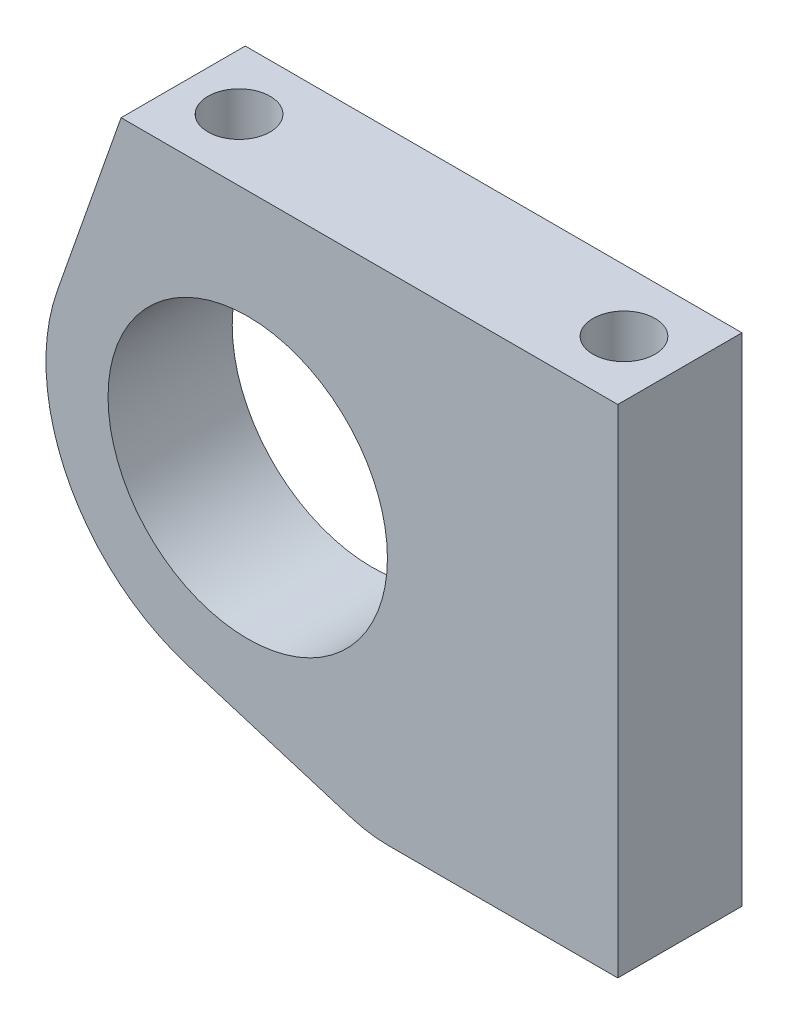
SolidWorks part; units mm, degrees
ref_plane "Front" through (0, 0, 0) normal (0, 0, 1) x (1, 0, 0)
ref_plane "Top" through (0, 0, 0) normal (0, 1, 0) x (1, 0, 0)
ref_plane "Right" through (0, 0, 0) normal (1, 0, 0) x (0, 0, -1)
sketch "Sketch1" plane through (0, 0, 0) normal (0, 0, 1) x (1, 0, 0)
  line L0 (0, 0) -> (50.8, 0) construction
  line L5 (0, 50.8) -> (50.8, 50.8)
  line L6 (0, 50.8) -> (-6.518, 32.2373)
  line L7 (50.8, 50.8) -> (50.8, 0)
  line L8 (50.8, 0) -> (27.3027, 0)
  line L9 (23.5809, 0.5576) -> (6.9061, 5.6686)
  circle A0 centre (12.954, 25.4) radius 6.35
  circle A1 centre (12.954, 25.4) radius 14.2875
  circle A2 centre (12.954, 25.4) radius 20.6375
  arc A3 (23.5809, 0.5576) -> (27.3027, 0) centre (27.3027, 12.7) ccw
  point P11 (12.954, 46.0375)
  point P20 (25.4, 0)
  dimension "D2" = 12.7
  dimension "D5" = 28.575
  dimension "D8" = 25.4
  dimension "D9" = 12.7
  dimension "D1" = 50.8
  dimension "D3" = 25.4
  dimension "D4" = 37.846
  dimension "D7" = 50.8
  dimension "D10" = 50.8
  dimension "D6" = 6.35
extrude "Boss-Extrude2" add sketch "Sketch1" along normal blind 12.7
sketch "Sketch3" plane through (0, 50.8, 0) normal (0, 1, 0) x (1, 0, 0)
  line L0 (0, -6.35) -> (50.8, -6.35) construction
  line L1 (0, -12.7) -> (0, 0) construction
  line L2 (50.8, -12.7) -> (50.8, 0) construction
  circle A0 centre (45.085, -6.35) radius 3.175
  circle A1 centre (5.715, -6.35) radius 3.175
  dimension "D1" = 6.35
  dimension "D2" = 5.715
  dimension "D3" = 5.715
extrude "Cut-Extrude2" cut sketch "Sketch3" against normal blind 12.7
